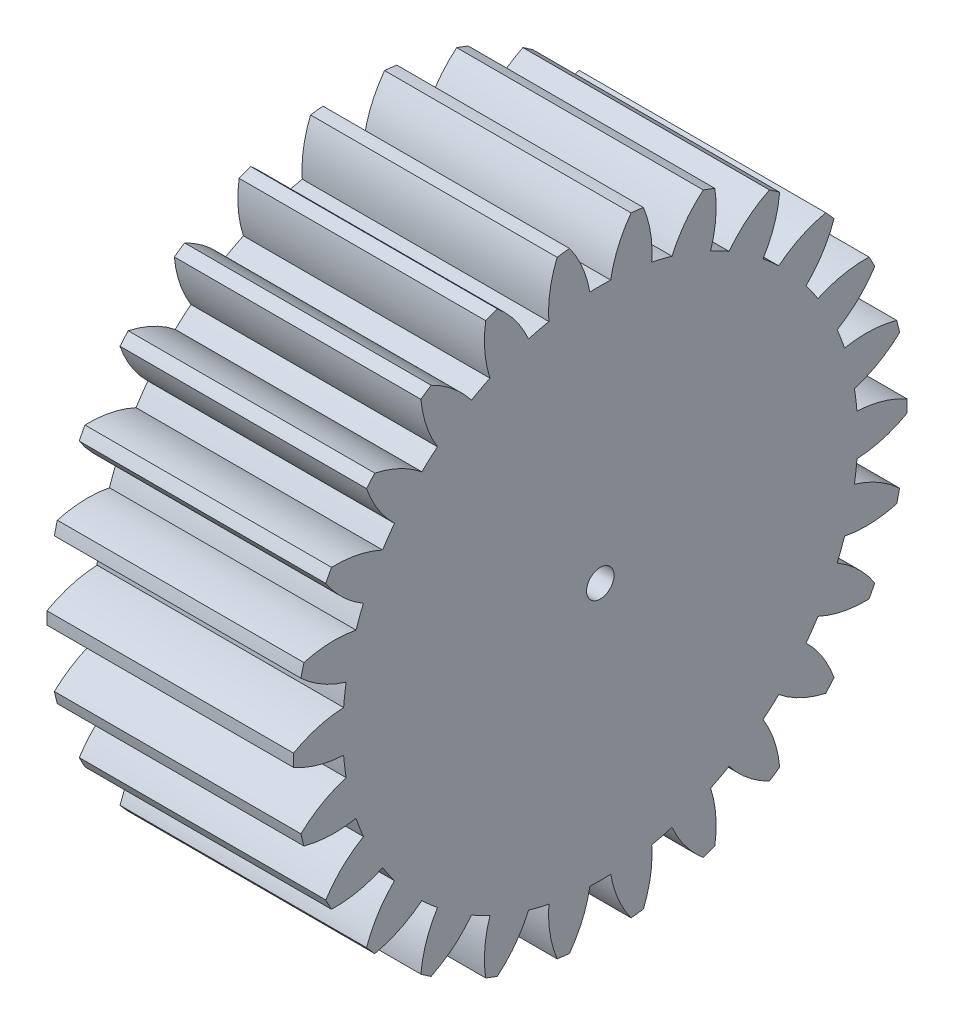
SolidWorks part; units mm, degrees
ref_plane "Plane1" through (0, 0, 0) normal (0, 0, 1) x (1, 0, 0)
ref_plane "Plane2" through (0, 0, 0) normal (0, 1, 0) x (1, 0, 0)
ref_plane "Plane3" through (0, 0, 0) normal (1, 0, 0) x (0, 0, -1)
other "Configuration Table"
sketch "HoldingSke" plane through (0, 0, 0) normal (0, 1, 0) x (1, 0, 0)
  line L0 (0, 0) -> (1.1235, -0.548)
  line L1 (-15, 0) -> (100, 0) construction
  line L2 (0, 0) -> (-2.1039, 2.3779)
  line L3 (0, 0) -> (-11.863, 4.5341)
  line L4 (0, 0) -> (7.762, 3.7858)
  line L5 (0, 0) -> (-46.8476, -17.4728)
  line L6 (0, 0) -> (-7.4607, -5.0337)
  line L7 (-2.1039, 2.3779) -> (8.6586, 51.2059)
  line L8 (-76.2, 54.61) -> (-76.1, 54.61)
  line L9 (-71.009, 38.7566) -> (-53.1078, 45.2721)
  line L10 (-76.2, 71.12) -> (104.1128, 71.12)
  line L11 (0, 0) -> (-9, 0)
  line L12 (-76.2, 101.6) -> (-76.17, 101.6)
  line L13 (24.9733, 27.94) -> (52.9518, 28.4284)
  line L14 (24.9733, 27.94) -> (24.9743, 27.94)
  line L15 (24.9733, 27.94) -> (100.4006, 29.5858)
  line L16 (-63.627, -0.8) -> (-12.827, -0.8)
  circle A0 centre (0, 0) radius 0.5
  circle A1 centre (0, 0) radius 9.399
  circle A2 centre (0, 0) radius 37.5
  circle A3 centre (0, 0) radius 0.5
  dimension "MHD" = 18.798
  dimension "Hub_dia" = 75
  dimension "Bore" = 1
  dimension "MBD" = 1
  dimension "Num_teeth" = 26
  dimension "Pitch" = 1.25
  dimension "Overall_len" = 50
  dimension "Show_teeth" = 26
  dimension "Thickness" = 9
  dimension "OAL" = 50.0001
  dimension "T_dim" = 0.1
  dimension "Ap" = 20
  dimension "H" = 19.05
  dimension "Pitch_radius" = 180.3128
  dimension "Width" = 9
  dimension "Backlash" = 0.03
  dimension "Addendum_fac" = 1
  dimension "Dedendum_fac" = 1.25
  dimension "Clearance_fac" = 0.25
  dimension "Dedendum_add" = 0.001
  dimension "Module" = 0.8
sketch "BasProSke" plane through (0, 0, 0) normal (0, 1, 0) x (1, 0, 0)
  line L0 (-10, 0) -> (60, 0) construction
  line L1 (0, 0) -> (0, 11.2)
  line L2 (0, 0) -> (9, 0)
  line L3 (9, 0) -> (9, 11.2)
  line L4 (9, 11.2) -> (0, 11.2)
  dimension "Thickness" = 9
  dimension "Diameter" = 22.4
revolve "Base-Revolve" add sketch "BasProSke" angle 360 about L0
sketch "TooCutSke" plane through (0, 0, 0) normal (1, 0, 0) x (0, 0, -1)
  line L1 (0, 0) -> (0, 107) construction
  line L2 (0, 0) -> (-0.6804, 10.3777) construction
  line L3 (0, 0) -> (-2.5033, 20.6167) construction
  line L4 (-0.6804, 10.3777) -> (-1.2517, 10.3084) construction
  arc A0 (0.3809, 9.3913) -> (-0.3809, 9.3913) centre (0, 0) ccw
  arc A1 (1.1421, 11.1672) -> (-1.1421, 11.1672) centre (0, 0) ccw
  circle A2 centre (0, 0) radius 10.4 construction
  circle A3 centre (0, 0) radius 9.7728 construction
  arc A4 (-0.3809, 9.3913) -> (-1.1421, 11.1672) centre (-4.4805, 8.6852) ccw
  arc A5 (1.1421, 11.1672) -> (0.3809, 9.3913) centre (4.4805, 8.6852) ccw
  dimension "Root_dia" = 18.798
  dimension "Overcut_dia" = 22.4508
  dimension "Pitch_dia" = 20.8
  dimension "Base_dia" = 19.5456
  dimension "Flank_rad" = 4.16
  dimension "Half_ang" = 6.923
  dimension "Half_CT" = 0.5754
extrude "ToothCut" cut sketch "TooCutSke" along normal through all
fillet "Breaks" [suppressed] radius 0.016
fillet "RootFillets" [suppressed] radius 0.201
pattern_circular "TeethCuts" count 26 every 13.846 about axis through (-10, 0, 0) along (1, 0, 0) of "ToothCut", "RootFillets", "Breaks"
sketch "HubNeaOneSke" plane through (0, 0, 0) normal (-1, 0, 0) x (0, 0, 1)
  circle A0 centre (0, 0) radius 9.399
  dimension "Diameter" = 18.798
extrude "HubNearOne" [suppressed] add sketch "HubNeaOneSke" along normal blind 41.0001
sketch "HubNeaBotSke" plane through (0, 0, 0) normal (-1, 0, 0) x (0, 0, 1)
  circle A0 centre (0, 0) radius 9.399
  dimension "Diameter" = 18.798
extrude "HubNearBoth" [suppressed] add sketch "HubNeaBotSke" along normal blind 20.5
ref_plane "FarPln" through (9, 0, 0) normal (1, 0, 0) x (0, 0, -1)
sketch "HubFarSke" plane through (9, 0, 0) normal (1, 0, 0) x (0, 0, -1)
  circle A0 centre (0, 0) radius 9.399
  dimension "Diameter" = 18.798
extrude "HubFar" [suppressed] add sketch "HubFarSke" along normal blind 20.5
sketch "BorSke" plane through (0, 0, 0) normal (1, 0, 0) x (0, 0, -1)
  circle A0 centre (0, 0) radius 0.5
  dimension "Diameter" = 1
extrude "Bore" cut sketch "BorSke" along normal mid plane 100.0001
sketch "KeySke" plane through (0, 0, 0) normal (1, 0, 0) x (0, 0, -1)
  line L0 (-0.05, 0) -> (-0.05, 0.6)
  line L1 (-0.05, 0.6) -> (0.05, 0.6)
  line L2 (0.05, 0.6) -> (0.05, 0)
  line L3 (0, 0) -> (0, 34) construction
  line L4 (-0.05, 0) -> (0.05, 0)
  dimension "Offset" = 0.6
  dimension "Width" = 0.1
extrude "Keyway" [suppressed] cut sketch "KeySke" along normal mid plane 100.0001
pattern_circular "Keyway2" [suppressed] count 2 every 90 about axis through (-10, 0, 0) along (1, 0, 0)
equation "' \"Module@HoldingSke\" = 6.35"
equation "' \"Num_teeth@HoldingSke\" = 12"
equation "' \"Ap@HoldingSke\" =  20"
equation "' \"Ap@HoldingSke\" = 20"
equation "' \"Width@HoldingSke\" = 0.5 * 25.4"
equation "' \"Hub_dia@HoldingSke\"= 1 * 25.4"
equation "' \"Hub_dia@HoldingSke\" = 1 * 25.4"
equation "' \"Overall_len@HoldingSke\" = 1.0 * 25.4"
equation "' \"Bore@HoldingSke\" = 0.75 * 25.4"
equation "' \"T_dim@HoldingSke\" = 0.1 * 25.4"
equation "' \"Width@KeySke\" = 0.25 * 25.4"
equation "' \"Show_teeth@HoldingSke\" = 13"
equation "' \"Backlash@HoldingSke\" = 0.009 * 25.4"
equation "' \"Addendum_fac@HoldingSke\" = 1.0"
equation "' \"Dedendum_fac@HoldingSke\" = 1.25"
equation "' \"Dedendum_add@HoldingSke\" = 0.00005 * 25.4"
equation "' \"Clearance_fac@HoldingSke\" = 0.25"
equation "\"Pitch@HoldingSke\" = 1 / \"Module@HoldingSke\""
equation "\"Overcut_dia@TooCutSke\" = (\"Num_teeth@HoldingSke\" + 2 * \"Addendum_fac@HoldingSke\") / \"Pitch@HoldingSke\" + 0.002 * 25.4"
equation "\"Pitch_dia@TooCutSke\" = \"Num_teeth@HoldingSke\" / \"Pitch@HoldingSke\""
equation "\"Base_dia@TooCutSke\" = \"Num_teeth@HoldingSke\" / \"Pitch@HoldingSke\" * cos((\"Ap@HoldingSke\"  * 3.14159265 / 180))"
equation "\"Root_dia@TooCutSke\" = (\"Num_teeth@HoldingSke\" + 2) / \"Pitch@HoldingSke\" - 2 * (\"Addendum_fac@HoldingSke\" + \"Dedendum_fac@HoldingSke\") / \"Pitch@HoldingSke\" - \"Dedendum_add@HoldingSke\" * 2"
equation "\"Half_ang@TooCutSke\" = 180 / \"Num_teeth@HoldingSke\""
equation "\"Half_CT@TooCutSke\" = \"Num_teeth@HoldingSke\" / \"Pitch@HoldingSke\" * sin((3.14159265 / 2 / \"Num_teeth@HoldingSke\")) / 2 - 7 * \"Backlash@HoldingSke\" / 4"
equation "\"Flank_rad@TooCutSke\" = \"Num_teeth@HoldingSke\" / \"Pitch@HoldingSke\" / 5"
equation "\"Radius@RootFillets\" = \"Clearance_fac@HoldingSke\" / \"Pitch@HoldingSke\" + \"Dedendum_add@HoldingSke\""
equation "\"Break_rad@Breaks\" = 0.02 / \"Pitch@HoldingSke\""
equation "\"Thickness@HoldingSke\" = \"Width@HoldingSke\""
equation "\"OAL@HoldingSke\" = \"Thickness@HoldingSke\""
equation "\"MHD@HoldingSke\" = (\"Num_teeth@HoldingSke\" + 2) / \"Pitch@HoldingSke\" - 2 * (\"Addendum_fac@HoldingSke\" + \"Dedendum_fac@HoldingSke\")  / \"Pitch@HoldingSke\" - \"Dedendum_add@HoldingSke\" * 2"
equation "\"MBD@HoldingSke\" = (\"Num_teeth@HoldingSke\" + 2) / \"Pitch@HoldingSke\" - 2 * (\"Addendum_fac@HoldingSke\" + \"Dedendum_fac@HoldingSke\")  / \"Pitch@HoldingSke\" - \"Dedendum_add@HoldingSke\" * 2 - 0.002 * 25.4"
equation "\"MHD@HoldingSke\" = ((sgn( \"MHD@HoldingSke\" - \"Hub_dia@HoldingSke\" )-1)*( \"MHD@HoldingSke\" - \"Hub_dia@HoldingSke\" ))/-2+ \"Hub_dia@HoldingSke\""
equation "\"MBD@HoldingSke\" = ((sgn( \"MBD@HoldingSke\" - \"Bore@HoldingSke\" )-1)*( \"MBD@HoldingSke\" - \"Bore@HoldingSke\" ))/-2+ \"Bore@HoldingSke\""
equation "\"OAL@HoldingSke\" = ((sgn( \"OAL@HoldingSke\" - \"Overall_len@HoldingSke\" )+1)*( \"OAL@HoldingSke\" - \"Overall_len@HoldingSke\" ))/2 + \"Overall_len@HoldingSke\" + 0.000002 * 25.4"
equation "\"Num_teeth@TeethCuts\" = int( \"Show_teeth@HoldingSke\" ) + 1"
equation "\"Num_teeth@TeethCuts\" = ((sgn( \"Num_teeth@TeethCuts\" - \"Num_teeth@HoldingSke\" )-1)*( \"Num_teeth@TeethCuts\" - \"Num_teeth@HoldingSke\" ))/-2+ \"Num_teeth@HoldingSke\""
equation "\"Num_teeth@TeethCuts\" = ((sgn( \"Num_teeth@TeethCuts\" - 2.0)+1)*( \"Num_teeth@TeethCuts\" - 2.0))/2 +2.0"
equation "\"Angle@TeethCuts\" = 360.0 / \"Num_teeth@HoldingSke\""
equation "\"Diameter@BasProSke\" = (\"Num_teeth@HoldingSke\" + 2 * \"Addendum_fac@HoldingSke\") / \"Pitch@HoldingSke\""
equation "\"Thickness@BasProSke\"  = \"Thickness@HoldingSke\""
equation "' \"Fillet_rad@BasProSke\" =  \"Thickness@HoldingSke\" * 0.05"
equation "' \"Fillet_rad@BasProSke\" = \"Thickness@HoldingSke\" * 0.05"
equation "\"MHD@HoldingSke\" = ((sgn( \"MHD@HoldingSke\" - \"Root_dia@TooCutSke\" )-1)*( \"MHD@HoldingSke\" - \"Root_dia@TooCutSke\" ))/-2+ \"Root_dia@TooCutSke\""
equation "\"Diameter@HubNeaOneSke\" = \"MHD@HoldingSke\""
equation "\"Length@HubNearOne\" = \"OAL@HoldingSke\" - \"Thickness@BasProSke\""
equation "\"Diameter@HubNeaBotSke\" = \"MHD@HoldingSke\""
equation "\"Length@HubNearBoth\" = ( \"OAL@HoldingSke\" - \"Thickness@BasProSke\" ) / 2.0"
equation "\"Thickness@FarPln\" = \"Thickness@BasProSke\""
equation "\"Diameter@HubFarSke\" = \"MHD@HoldingSke\""
equation "\"Length@HubFar\" = ( \"OAL@HoldingSke\" - \"Thickness@BasProSke\" ) / 2.0"
equation "\"Diameter@BorSke\" = \"MBD@HoldingSke\""
equation "\"D1@Bore\" = \"OAL@HoldingSke\" * 2.0"
equation "\"D1@Keyway\" = \"OAL@HoldingSke\" * 2.0"
equation "\"Offset@KeySke\" = \"T_dim@HoldingSke\" + \"MBD@HoldingSke\" / 2.0"
